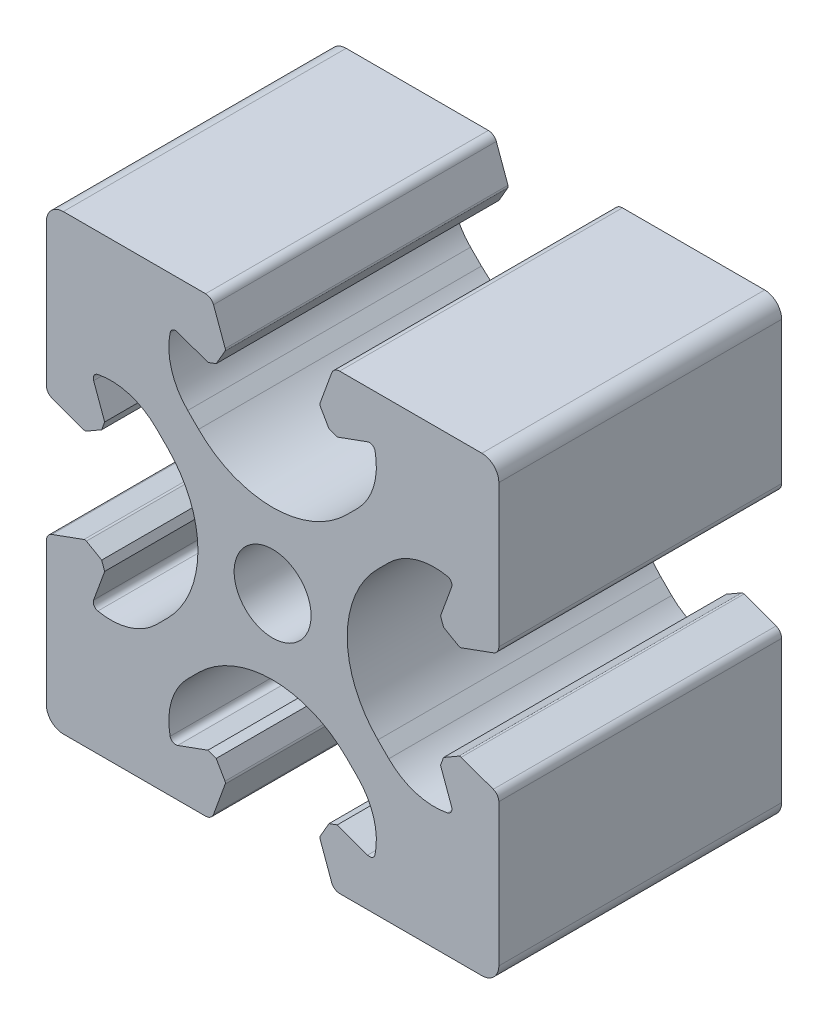
SolidWorks part; units mm, degrees
material "6005-T5"
ref_plane "Front" through (0, 0, 0) normal (0, 0, 1) x (1, 0, 0)
ref_plane "Top" through (0, 0, 0) normal (0, 1, 0) x (1, 0, 0)
ref_plane "Right" through (0, 0, 0) normal (1, 0, 0) x (0, 0, -1)
sketch "Sk Main Extrusion" plane through (0, 0, 0) normal (0, 0, 1) x (1, 0, 0)
  line L5 (4.1901, -16.6712) -> (5.2221, -19.5065)
  line L6 (5.9268, -20) -> (18.5, -20)
  line L7 (20, -18.5) -> (20, -5.9268)
  line L8 (19.5065, -5.2221) -> (16.6712, -4.1901)
  line L9 (16.4607, -4.2085) -> (15.1113, -4.9876)
  line L10 (15.1113, -4.9876) -> (14.8453, -5.7185)
  line L11 (14.8453, -5.7185) -> (15.8198, -8.3962)
  line L12 (10.2727, -7.5042) -> (9.3093, -6.5407)
  line L13 (9.3093, 6.5407) -> (10.2727, 7.5042)
  line L14 (15.8198, 8.3962) -> (14.8453, 5.7185)
  line L15 (14.8453, 5.7185) -> (15.1113, 4.9876)
  line L16 (15.1113, 4.9876) -> (16.4607, 4.2085)
  line L17 (16.6712, 4.1901) -> (19.5065, 5.2221)
  line L18 (20, 5.9268) -> (20, 18.5)
  line L19 (18.5, 20) -> (5.9268, 20)
  line L20 (5.2221, 19.5065) -> (4.1901, 16.6712)
  line L21 (4.2085, 16.4607) -> (4.9876, 15.1113)
  line L22 (4.9876, 15.1113) -> (5.7185, 14.8453)
  line L23 (5.7185, 14.8453) -> (8.3962, 15.8198)
  line L24 (7.5042, 10.2727) -> (6.5407, 9.3093)
  line L25 (-6.5407, 9.3093) -> (-7.5042, 10.2727)
  line L26 (-8.3962, 15.8198) -> (-5.7185, 14.8453)
  line L27 (-5.7185, 14.8453) -> (-4.9876, 15.1113)
  line L28 (-4.9876, 15.1113) -> (-4.2085, 16.4607)
  line L29 (-4.1901, 16.6712) -> (-5.2221, 19.5065)
  line L30 (-5.9268, 20) -> (-18.5, 20)
  line L31 (-20, 18.5) -> (-20, 5.9268)
  line L32 (-19.5065, 5.2221) -> (-16.6712, 4.1901)
  line L33 (-16.4607, 4.2085) -> (-15.1113, 4.9876)
  line L34 (-15.1113, 4.9876) -> (-14.8453, 5.7185)
  line L35 (-14.8453, 5.7185) -> (-15.8198, 8.3962)
  line L36 (-10.2727, 7.5042) -> (-9.3093, 6.5407)
  line L37 (-9.3093, -6.5407) -> (-10.2727, -7.5042)
  line L38 (-15.8198, -8.3962) -> (-14.8453, -5.7185)
  line L39 (-14.8453, -5.7185) -> (-15.1113, -4.9876)
  line L40 (-15.1113, -4.9876) -> (-16.4607, -4.2085)
  line L41 (-16.6712, -4.1901) -> (-19.5065, -5.2221)
  line L42 (-20, -5.9268) -> (-20, -18.5)
  line L43 (-18.5, -20) -> (-5.9268, -20)
  line L44 (-5.2221, -19.5065) -> (-4.1901, -16.6712)
  line L45 (-4.2085, -16.4607) -> (-4.9876, -15.1113)
  line L46 (-4.9876, -15.1113) -> (-5.7185, -14.8453)
  line L47 (-5.7185, -14.8453) -> (-8.3962, -15.8198)
  line L48 (-7.5042, -10.2727) -> (-6.5407, -9.3093)
  line L49 (6.5407, -9.3093) -> (7.5042, -10.2727)
  line L50 (8.3962, -15.8198) -> (5.7185, -14.8453)
  line L51 (5.7185, -14.8453) -> (4.9876, -15.1113)
  line L52 (4.9876, -15.1113) -> (4.2085, -16.4607)
  circle A0 centre (0, 0) radius 3.4
  arc A1 (5.2221, -19.5065) -> (5.9268, -20) centre (5.9268, -19.25) ccw
  arc A2 (18.5, -20) -> (20, -18.5) centre (18.5, -18.5) ccw
  arc A3 (20, -5.9268) -> (19.5065, -5.2221) centre (19.25, -5.9268) ccw
  arc A4 (16.6712, -4.1901) -> (16.4607, -4.2085) centre (16.5857, -4.425) ccw
  arc A5 (15.4507, -9.057) -> (15.8198, -8.3962) centre (15.35, -8.5672) ccw
  arc A6 (10.2727, -7.5042) -> (15.4507, -9.057) centre (14.3032, -3.4737) ccw
  arc A7 (9.3093, 6.5407) -> (9.3093, -6.5407) centre (15.85, 0) ccw
  arc A8 (15.4507, 9.057) -> (10.2727, 7.5042) centre (14.3032, 3.4737) ccw
  arc A9 (15.8198, 8.3962) -> (15.4507, 9.057) centre (15.35, 8.5672) ccw
  arc A10 (16.4607, 4.2085) -> (16.6712, 4.1901) centre (16.5857, 4.425) ccw
  arc A11 (19.5065, 5.2221) -> (20, 5.9268) centre (19.25, 5.9268) ccw
  arc A12 (20, 18.5) -> (18.5, 20) centre (18.5, 18.5) ccw
  arc A13 (5.9268, 20) -> (5.2221, 19.5065) centre (5.9268, 19.25) ccw
  arc A14 (4.1901, 16.6712) -> (4.2085, 16.4607) centre (4.425, 16.5857) ccw
  arc A15 (9.057, 15.4507) -> (8.3962, 15.8198) centre (8.5672, 15.35) ccw
  arc A16 (7.5042, 10.2727) -> (9.057, 15.4507) centre (3.4737, 14.3032) ccw
  arc A17 (-6.5407, 9.3093) -> (6.5407, 9.3093) centre (0, 15.85) ccw
  arc A18 (-9.057, 15.4507) -> (-7.5042, 10.2727) centre (-3.4737, 14.3032) ccw
  arc A19 (-8.3962, 15.8198) -> (-9.057, 15.4507) centre (-8.5672, 15.35) ccw
  arc A20 (-4.2085, 16.4607) -> (-4.1901, 16.6712) centre (-4.425, 16.5857) ccw
  arc A21 (-5.2221, 19.5065) -> (-5.9268, 20) centre (-5.9268, 19.25) ccw
  arc A22 (-18.5, 20) -> (-20, 18.5) centre (-18.5, 18.5) ccw
  arc A23 (-20, 5.9268) -> (-19.5065, 5.2221) centre (-19.25, 5.9268) ccw
  arc A24 (-16.6712, 4.1901) -> (-16.4607, 4.2085) centre (-16.5857, 4.425) ccw
  arc A25 (-15.4507, 9.057) -> (-15.8198, 8.3962) centre (-15.35, 8.5672) ccw
  arc A26 (-10.2727, 7.5042) -> (-15.4507, 9.057) centre (-14.3032, 3.4737) ccw
  arc A27 (-9.3093, -6.5407) -> (-9.3093, 6.5407) centre (-15.85, 0) ccw
  arc A28 (-15.4507, -9.057) -> (-10.2727, -7.5042) centre (-14.3032, -3.4737) ccw
  arc A29 (-15.8198, -8.3962) -> (-15.4507, -9.057) centre (-15.35, -8.5672) ccw
  arc A30 (-16.4607, -4.2085) -> (-16.6712, -4.1901) centre (-16.5857, -4.425) ccw
  arc A31 (-19.5065, -5.2221) -> (-20, -5.9268) centre (-19.25, -5.9268) ccw
  arc A32 (-20, -18.5) -> (-18.5, -20) centre (-18.5, -18.5) ccw
  arc A33 (-5.9268, -20) -> (-5.2221, -19.5065) centre (-5.9268, -19.25) ccw
  arc A34 (-4.1901, -16.6712) -> (-4.2085, -16.4607) centre (-4.425, -16.5857) ccw
  arc A35 (-9.057, -15.4507) -> (-8.3962, -15.8198) centre (-8.5672, -15.35) ccw
  arc A36 (-7.5042, -10.2727) -> (-9.057, -15.4507) centre (-3.4737, -14.3032) ccw
  arc A37 (6.5407, -9.3093) -> (-6.5407, -9.3093) centre (0, -15.85) ccw
  arc A38 (9.057, -15.4507) -> (7.5042, -10.2727) centre (3.4737, -14.3032) ccw
  arc A39 (8.3962, -15.8198) -> (9.057, -15.4507) centre (8.5672, -15.35) ccw
  arc A40 (4.2085, -16.4607) -> (4.1901, -16.6712) centre (4.425, -16.5857) ccw
extrude "Main Extrusion" add sketch "Sk Main Extrusion" against normal blind 25
sketch "Threaded Insert Mate Sketch" plane through (0, 0, 0) normal (0, 0, 1) x (1, 0, 0)
  circle A0 centre (0, 12.7) radius 5.6515
  circle A1 centre (12.7, 0) radius 5.6515
  circle A2 centre (0, -12.7) radius 5.6515
  circle A3 centre (-12.7, 0) radius 5.6515
  circle A4 centre (0, 0) radius 3.4 construction
  point P12 (0, 0)
  dimension "D2" = 11.303
  dimension "D1" = 12.7
  dimension "D3" = 4
equation "\"Weight kg\"= round ( \"SW-Mass\" , 2 )"
equation "\"Weight lbs\"= round ( \"SW-Mass\" * 2.2046 , 2 )"
equation "\"Length mm\"= round ( \"Length@Main Extrusion\" , 2 )"
equation "\"Length in\"= round ( \"Length@Main Extrusion\" / 25.4 , 3 )"
